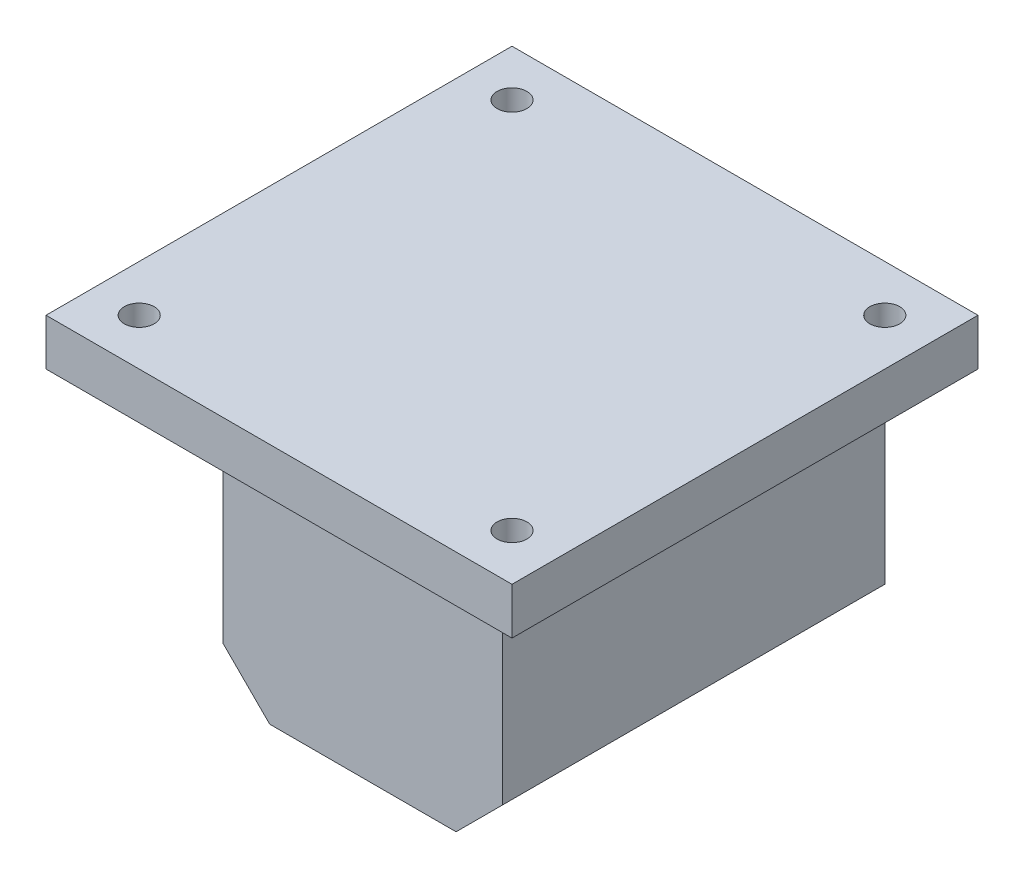
SolidWorks part; units mm, degrees
ref_plane "Front Plane" through (0, 0, 0) normal (0, 0, 1) x (1, 0, 0)
ref_plane "Top Plane" through (0, 0, 0) normal (0, 1, 0) x (1, 0, 0)
ref_plane "Right Plane" through (0, 0, 0) normal (1, 0, 0) x (0, 0, -1)
sketch "Sketch1" plane through (0, 0, 0) normal (0, 0, 1) x (1, 0, 0)
  line L1 (-15, -15) -> (15, -15)
  line L2 (-15, -15) -> (-15, 15)
  line L3 (-15, 15) -> (15, 15)
  line L4 (15, -15) -> (15, 15)
  line L5 (-15, -15) -> (15, 15) construction
  line L6 (-15, 15) -> (15, -15) construction
  circle A0 centre (0, 0) radius 2.65
  dimension "D1" = 5.3
  dimension "D2" = 30
  dimension "D3" = 30
extrude "Boss-Extrude1" add sketch "Sketch1" along normal blind 31
sketch "Sketch2" plane through (0, 0, 31) normal (0, 0, 1) x (1, 0, 0)
  line L1 (15, -15) -> (-15, -15)
  line L2 (15, -15) -> (15, 15)
  line L3 (15, 15) -> (-15, 15)
  line L4 (-15, -15) -> (-15, 15)
  line L5 (15, -15) -> (-15, 15) construction
  line L6 (15, 15) -> (-15, -15) construction
  point P0 (0, 0)
extrude "Boss-Extrude2" add sketch "Sketch2" along normal blind 10
sketch "Sketch3" plane through (0, 15, 0) normal (0, 1, 0) x (1, 0, 0)
  line L0 (0, 0) -> (-25, 0)
  line L1 (15, 0) -> (-15, 0) construction
  line L2 (-25, 0) -> (-25, -50)
  line L3 (-25, -50) -> (25, -50)
  line L4 (25, -50) -> (25, 0)
  line L5 (25, 0) -> (0, 0)
  dimension "D1" = 25
  dimension "D2" = 50
  dimension "D3" = 50
  dimension "D4" = 50
extrude "Boss-Extrude3" add sketch "Sketch3" along normal blind 5
chamfer "Chamfer1" distance 5 angle 45 2 edges at (15, -15, 20.5) (-15, -15, 20.5)
sketch "Sketch4" plane through (0, 20, 0) normal (0, 1, 0) x (1, 0, 0)
  line L0 (-25, 0) -> (25, -50) construction
  line L2 (20, -45) -> (-20, -45) construction
  line L3 (20, -45) -> (20, -5) construction
  line L4 (20, -5) -> (-20, -5) construction
  line L5 (-20, -45) -> (-20, -5) construction
  line L6 (20, -45) -> (-20, -5) construction
  line L7 (20, -5) -> (-20, -45) construction
  circle A0 centre (-20, -5) radius 1.6
  circle A1 centre (20, -5) radius 1.6
  circle A2 centre (20, -45) radius 1.6
  circle A3 centre (-20, -45) radius 1.6
  point P4 (0, -25)
  dimension "D3" = 3.2
  dimension "D1" = 40
  dimension "D2" = 40
  dimension "D4" = 2
  dimension "D5" = 2
extrude "Cut-Extrude1" cut sketch "Sketch4" against normal up to next
